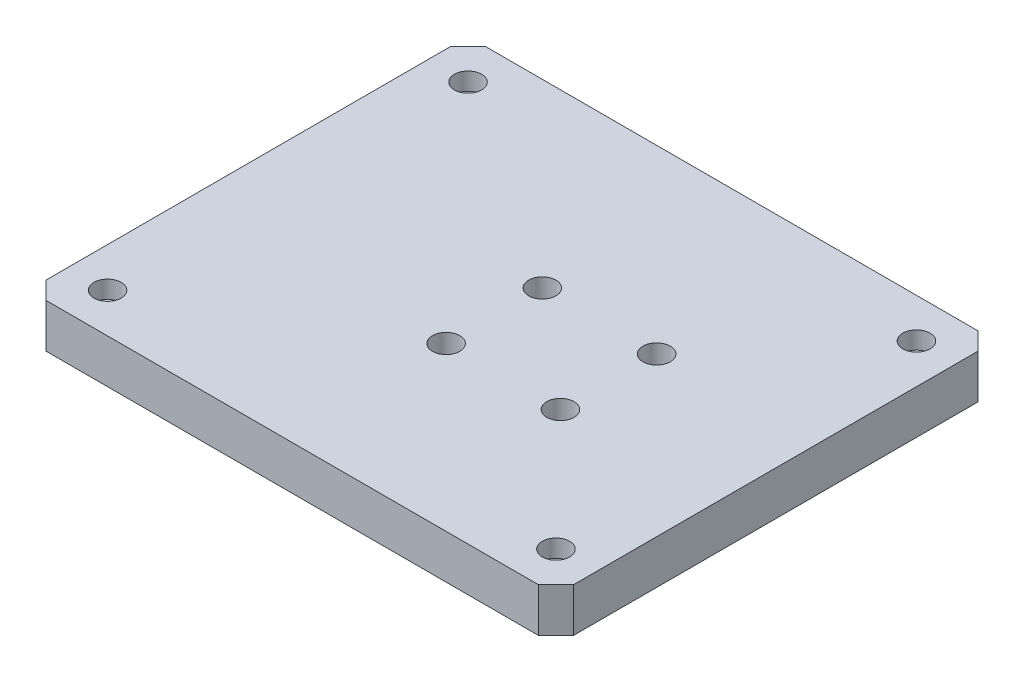
SolidWorks part; units mm, degrees
ref_plane "Front Plane" through (0, 0, 0) normal (0, 0, 1) x (1, 0, 0)
ref_plane "Top Plane" through (0, 0, 0) normal (0, 1, 0) x (1, 0, 0)
ref_plane "Right Plane" through (0, 0, 0) normal (1, 0, 0) x (0, 0, -1)
sketch "Sketch1" plane through (0, 0, 0) normal (0, 1, 0) x (1, 0, 0)
  line L1 (0, 0) -> (60, 0)
  line L2 (0, 0) -> (0, 50)
  line L3 (0, 50) -> (60, 50)
  line L4 (60, 0) -> (60, 50)
  dimension "D1" = 50
  dimension "D2" = 60
extrude "Boss-Extrude1" add sketch "Sketch1" along normal blind 5
chamfer "Chamfer1" distance 2 angle 45 4 edges at (60, 2.5, 0) (60, 2.5, -50) (0, 2.5, 0) (0, 2.5, -50)
sketch "Sketch2" plane through (0, 5, 0) normal (0, 1, 0) x (1, 0, 0)
  circle A1 centre (55.5, 4.5) radius 1.55
  circle A2 centre (55.5, 4.5) radius 1.55
  circle A3 centre (4.5, 4.5) radius 1.55
  circle A4 centre (4.5, 4.5) radius 1.55
  circle A5 centre (4.5, 45.5) radius 1.55
  circle A6 centre (4.5, 45.5) radius 1.55
  circle A7 centre (55.5, 45.5) radius 1.55
  circle A8 centre (55.5, 45.5) radius 1.55
  dimension "D1" = 0
  dimension "D2" = 0
  dimension "D3" = 0
  dimension "D4" = 0
extrude "Cut-Extrude1" cut sketch "Sketch2" against normal blind 2
sketch "Sketch3" plane through (0, 5, 0) normal (0, 1, 0) x (1, 0, 0)
  circle A1 centre (42, 29.4461) radius 1.55
  circle A2 centre (42, 29.4461) radius 1.55
  circle A3 centre (29, 29.4461) radius 1.55
  circle A4 centre (29, 29.4461) radius 1.55
  circle A5 centre (42, 18.509) radius 1.55
  circle A6 centre (42, 18.509) radius 1.55
  circle A7 centre (29, 18.509) radius 1.55
  circle A8 centre (29, 18.509) radius 1.55
  dimension "D1" = 0
  dimension "D2" = 0
  dimension "D3" = 0
  dimension "D4" = 0
extrude "Cut-Extrude2" cut sketch "Sketch3" against normal up to next
